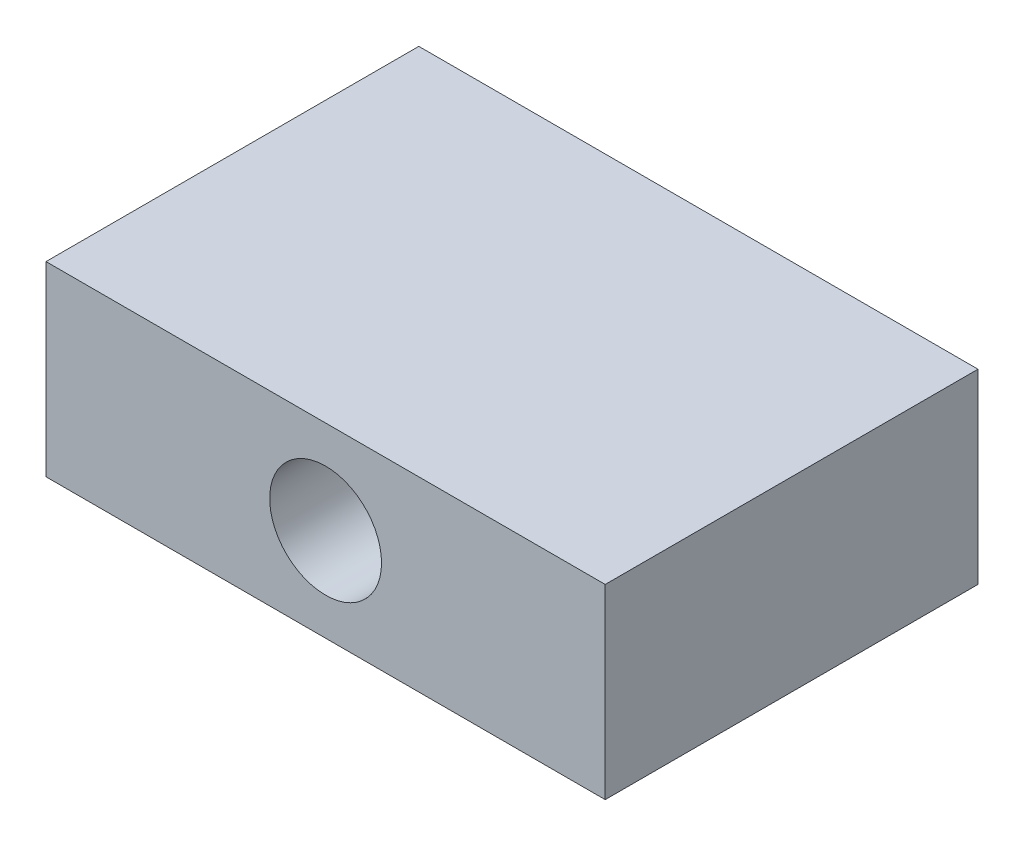
SolidWorks part; units mm, degrees
ref_plane "Ebene vorne" through (0, 0, 0) normal (0, 0, 1) x (1, 0, 0)
ref_plane "Ebene oben" through (0, 0, 0) normal (0, 1, 0) x (1, 0, 0)
ref_plane "Ebene rechts" through (0, 0, 0) normal (1, 0, 0) x (0, 0, -1)
sketch "Skizze1" plane through (0, 0, 0) normal (1, 0, 0) x (0, 0, -1)
  line L1 (0, 0) -> (20, 0)
  line L2 (0, 0) -> (0, 10)
  line L3 (0, 10) -> (20, 10)
  line L4 (20, 0) -> (20, 10)
  dimension "D1" = 20
  dimension "D2" = 10
extrude "Linear austragen1" add sketch "Skizze1" along normal blind 30
sketch "Skizze2" plane through (0, 0, 0) normal (0, 0, 1) x (1, 0, 0)
  line L1 (15, 5) -> (15, 10) construction
  line L4 (15, 5) -> (15, 0) construction
  line L8 (30, 10) -> (0, 10) construction
  line L9 (30, 0) -> (0, 0) construction
  line L10 (30, 10) -> (30, 0) construction
  circle A0 centre (15, 5) radius 3
  dimension "D2" = 6
  dimension "D1" = 15
extrude "Linear austragen2" cut sketch "Skizze2" against normal through all
